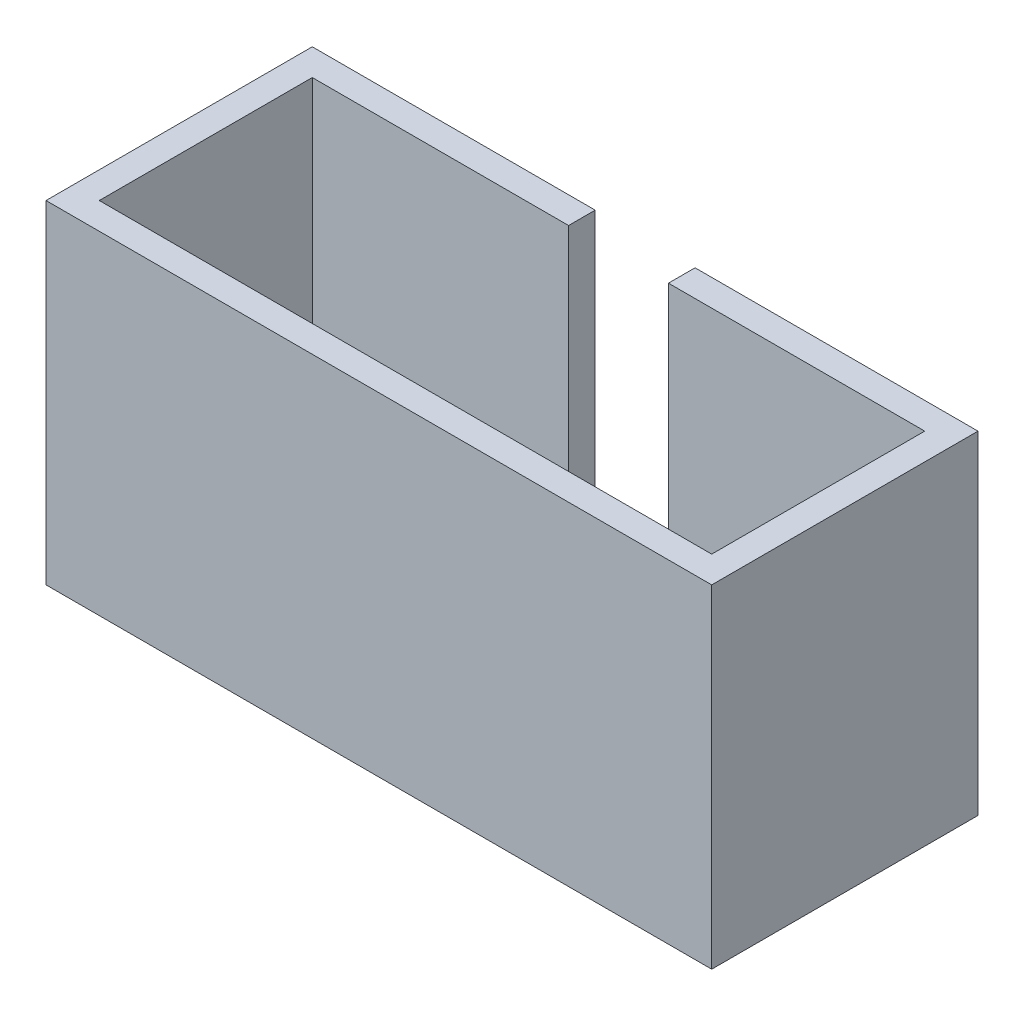
SolidWorks part; units mm, degrees
material "ABS"
ref_plane "Front Plane" through (0, 0, 0) normal (0, 0, 1) x (1, 0, 0)
ref_plane "Top Plane" through (0, 0, 0) normal (0, 1, 0) x (1, 0, 0)
ref_plane "Right Plane" through (0, 0, 0) normal (1, 0, 0) x (0, 0, -1)
ref_plane "Front Plane1" through (0, 0, -4) normal (0, 0, 1) x (1, 0, 0)
sketch "Sketch1" plane through (0, 0, 0) normal (0, 1, 0) x (1, 0, 0)
  line L0 (-10, 4) -> (10, -4) construction
  line L1 (-10, 4) -> (10, 4)
  line L2 (-10, 4) -> (-10, -4)
  line L3 (-10, -4) -> (10, -4)
  line L4 (10, 4) -> (10, -4)
  line L5 (9.2, 4) -> (9.2, 3.2) construction
  line L6 (9.2, 3.2) -> (10, 3.2) construction
  line L7 (-10, -3.2) -> (-9.2, -3.2) construction
  line L8 (-9.2, -3.2) -> (-9.2, -4) construction
  line L10 (-9.2, -3.2) -> (9.2, -3.2)
  line L11 (-9.2, -3.2) -> (-9.2, 3.2)
  line L12 (-9.2, 3.2) -> (9.2, 3.2)
  line L13 (9.2, -3.2) -> (9.2, 3.2)
  dimension "D1" = 20
  dimension "D2" = 8
  dimension "D3" = 0.8
  dimension "D4" = 0.8
  dimension "D5" = 0.8
  dimension "D6" = 0.8
extrude "Boss-Extrude1" add sketch "Sketch1" along normal blind 10
sketch "Sketch3" plane through (0, 0, 0) normal (0, 1, 0) x (1, 0, 0)
  line L1 (-9.2, 3.2) -> (9.2, 3.2)
  line L2 (-9.2, 3.2) -> (-9.2, -3.2)
  line L3 (-9.2, -3.2) -> (9.2, -3.2)
  line L4 (9.2, 3.2) -> (9.2, -3.2)
extrude "Boss-Extrude2" add sketch "Sketch3" along normal blind 0.8
sketch "Sketch2" plane through (0, 0, -4) normal (0, 0, 1) x (1, 0, 0)
  line L0 (-10, 2) -> (-1.5, 2) construction
  line L1 (-10, 10) -> (-10, 0) construction
  line L2 (10, 2) -> (1.5, 2) construction
  line L3 (10, 10) -> (10, 0) construction
  line L4 (-1.5, 2) -> (-1.5, 10)
  line L5 (-10, 10) -> (10, 10) construction
  line L6 (1.5, 2) -> (1.5, 10)
  line L7 (-1.5, 2) -> (1.5, 2)
  line L8 (-1.5, 10) -> (1.5, 10)
  dimension "D1" = 8.5
  dimension "D2" = 8.5
  dimension "D3" = 8
extrude "Cut-Extrude1" cut sketch "Sketch2" along normal up to next
